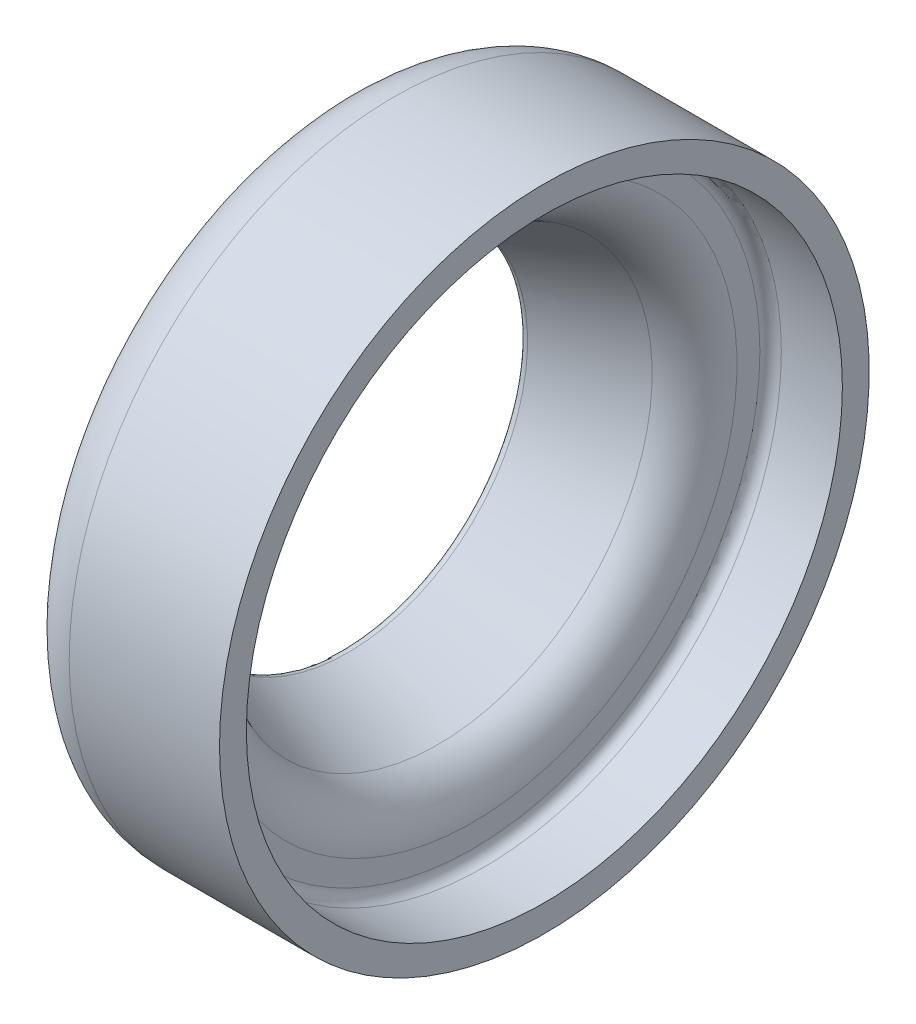
SolidWorks part; units mm, degrees
ref_plane "Front Plane" through (0, 0, 0) normal (0, 0, 1) x (1, 0, 0)
ref_plane "Top Plane" through (0, 0, 0) normal (0, 1, 0) x (1, 0, 0)
ref_plane "Right Plane" through (0, 0, 0) normal (1, 0, 0) x (0, 0, -1)
sketch "Sketch1" plane through (0, 0, 0) normal (0, 0, 1) x (1, 0, 0)
  line L0 (0, 0) -> (52.5618, 0) construction
  line L1 (0, 0) -> (0, 33) construction
  line L18 (0, 34.4494) -> (0, 50.5218)
  line L19 (10, 60.5218) -> (38, 60.5218)
  line L20 (38, 60.5218) -> (38, 55.5218)
  line L21 (38, 55.5218) -> (26.6314, 55.5218)
  line L22 (24.6314, 53.5218) -> (24.6314, 49.2527)
  line L23 (18.1814, 39.9041) -> (1.355, 33.5145)
  line L24 (21.6314, 55.5218) -> (13, 55.5218)
  line L25 (3, 45.5218) -> (3, 36.1598)
  line L26 (3, 36.1598) -> (15.0672, 40.5747)
  line L27 (21.6314, 49.9659) -> (21.6314, 55.5218)
  arc A6 (0, 50.5218) -> (10, 60.5218) centre (10, 50.5218) cw
  arc A7 (18.1814, 39.9041) -> (24.6314, 49.2527) centre (14.6314, 49.2527) ccw
  arc A8 (24.6314, 53.5218) -> (26.6314, 55.5218) centre (26.6314, 53.5218) cw
  arc A9 (0, 34.4494) -> (1.355, 33.5145) centre (1, 34.4494) ccw
  arc A10 (21.6314, 49.9659) -> (15.0672, 40.5747) centre (11.6314, 49.9659) cw
  arc A11 (13, 55.5218) -> (3, 45.5218) centre (13, 45.5218) ccw
  point P11 (0, 60.5218)
  point P27 (3, 55.5218)
  dimension "D3" = 10
  dimension "D4" = 10
  dimension "D5" = 2
  dimension "D7" = 10
  dimension "D8" = 19.3619
  dimension "D9" = 10
  dimension "D6" = 1
  dimension "D1" = 33
  dimension "D2" = 38
  dimension "D10" = 3
  dimension "D11" = 5
  dimension "D12" = 0.698
  dimension "D13" = 3
revolve "Revolve1" add sketch "Sketch1" angle 360 about L0
